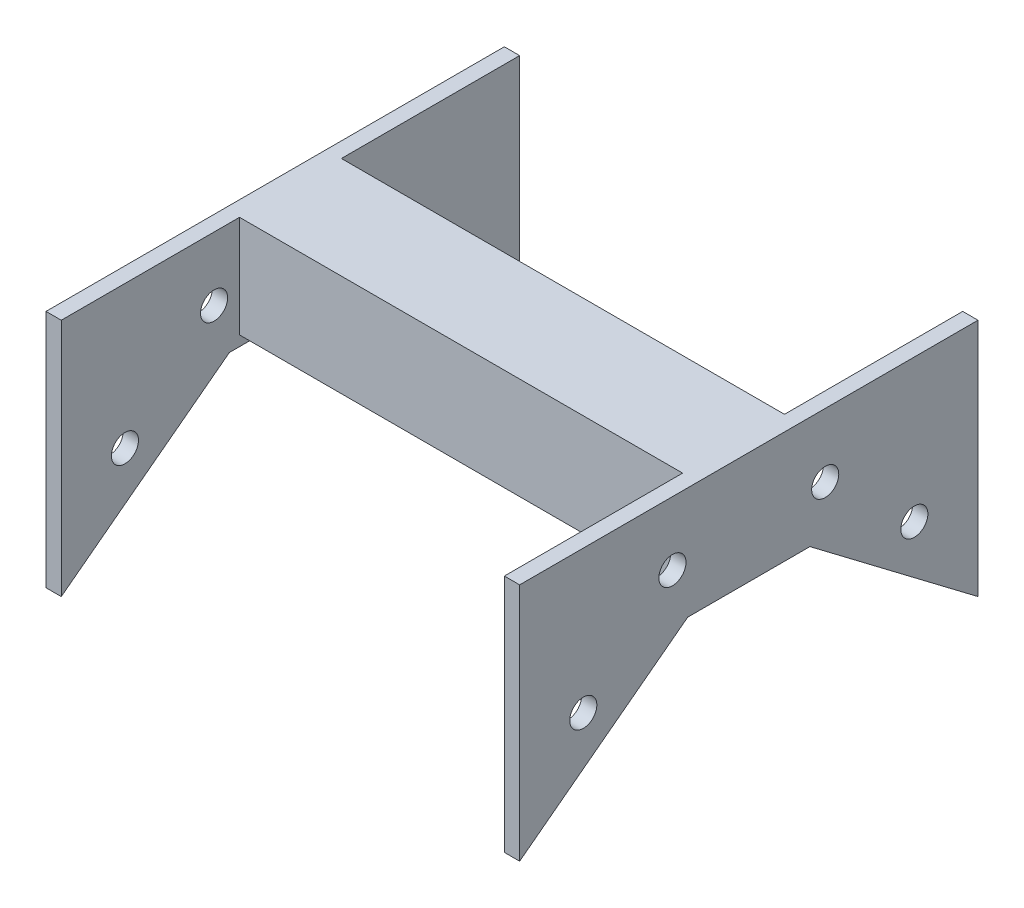
SolidWorks part; units mm, degrees
material "ABS"
ref_plane "Front Plane" through (0, 0, 0) normal (0, 0, 1) x (1, 0, 0)
ref_plane "Top Plane" through (0, 0, 0) normal (0, 1, 0) x (1, 0, 0)
ref_plane "Right Plane" through (0, 0, 0) normal (1, 0, 0) x (0, 0, -1)
sketch "Sketch2" plane through (0, 0, 0) normal (1, 0, 0) x (0, 0, -1)
  line L0 (0, 0) -> (0, 27.94) construction
  line L1 (15.24, 0) -> (-15.24, 0)
  line L2 (57.15, 27.94) -> (-57.15, 27.94)
  line L3 (-57.15, 27.94) -> (-57.15, -31.75)
  line L4 (-57.15, -31.75) -> (-15.24, 0)
  line L5 (57.15, -31.75) -> (15.24, 0)
  line L6 (57.15, 27.94) -> (57.15, -31.75)
  dimension "D1" = 27.94
  dimension "D2" = 57.15
  dimension "D3" = 15.24
  dimension "D4" = 31.75
extrude "Boss-Extrude1" add sketch "Sketch2" along normal blind 3.81
sketch "Sketch3" plane through (3.81, 0, 0) normal (1, 0, 0) x (0, 0, -1)
  line L0 (0, 0) -> (0, 27.94) construction
  line L1 (-15.24, 0) -> (15.24, 0) construction
  line L2 (57.15, 27.94) -> (-57.15, 27.94) construction
  line L3 (12.7, 27.94) -> (-12.7, 27.94)
  line L4 (-12.7, 27.94) -> (-12.7, 2.54)
  line L5 (-12.7, 2.54) -> (12.7, 2.54)
  line L6 (12.7, 27.94) -> (12.7, 2.54)
  point P10 (0, 2.54)
  dimension "D1" = 12.7
  dimension "D2" = 25.4
extrude "Boss-Extrude2" add sketch "Sketch3" along normal blind 55.245
sketch "Sketch4" plane through (0, 0, 0) normal (-1, 0, 0) x (0, 0, 1)
  line L0 (0, 0) -> (0, 38.3489) construction
  line L1 (-57.15, 27.94) -> (57.15, 27.94) construction
  line L2 (57.15, 27.94) -> (57.15, -31.75) construction
  circle A0 centre (19.05, 12.065) radius 3.3782
  circle A1 centre (41.275, -7.62) radius 3.3782
  circle A2 centre (-41.275, -7.62) radius 3.3782
  circle A3 centre (-19.05, 12.065) radius 3.3782
  dimension "D1" = 6.7564
  dimension "D4" = 6.7564
  dimension "D2" = 15.875
  dimension "D3" = 19.05
  dimension "D5" = 15.875
  dimension "D6" = 35.56
extrude "Cut-Extrude1" cut sketch "Sketch4" against normal blind 55.245
ref_plane "Plane1" through (59.055, 0, 0) normal (1, 0, 0) x (0, 0, -1)
mirror "Mirror1" about plane through (59.055, 0, 0) normal (1, 0, 0) of "Cut-Extrude1", "Boss-Extrude2", "Boss-Extrude1"
scale "Scale1" scale about centroid uniform scaling yes scale factor 1.02
